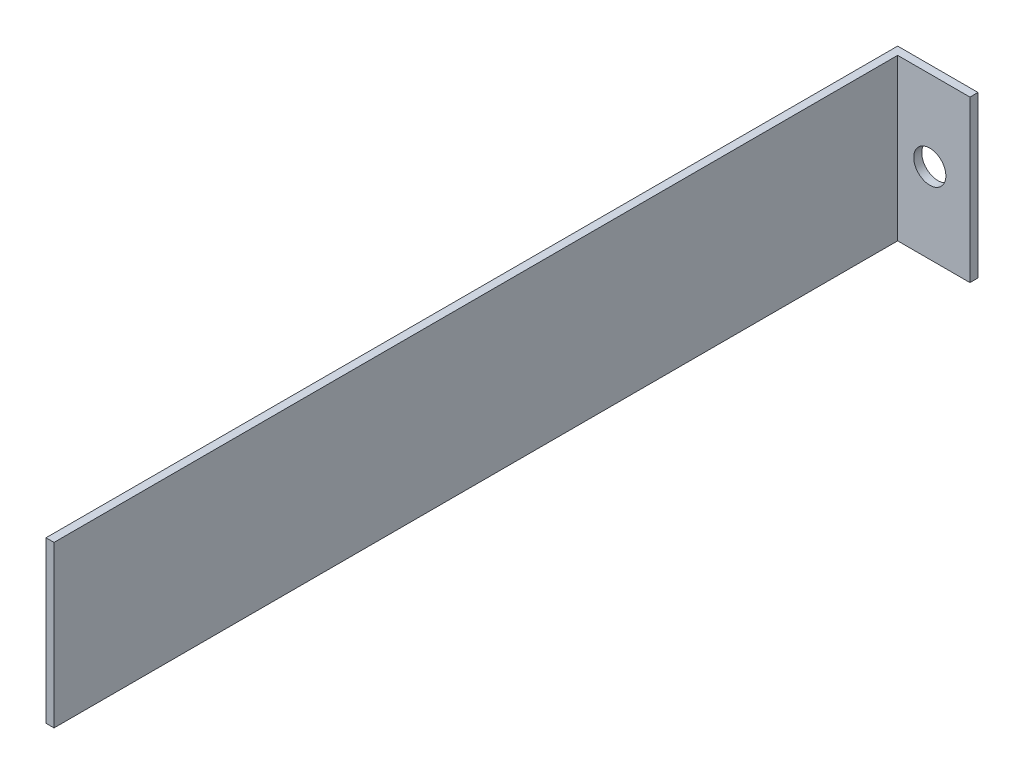
SolidWorks part; units mm, degrees
ref_plane "前视基准面" through (0, 0, 0) normal (0, 0, 1) x (1, 0, 0)
ref_plane "上视基准面" through (0, 0, 0) normal (0, 1, 0) x (1, 0, 0)
ref_plane "右视基准面" through (0, 0, 0) normal (1, 0, 0) x (0, 0, -1)
sketch "草图1" plane through (0, 0, 0) normal (0, 0, 1) x (1, 0, 0)
  line L0 (-37.1175, 25.838) -> (-17.1175, 25.838)
  line L1 (-17.1175, 25.838) -> (-17.1175, -14.162)
  line L2 (-17.1175, -14.162) -> (-37.1175, -14.162)
  line L3 (-37.1175, -14.162) -> (-37.1175, 25.838)
  line L4 (-27.1175, 25.838) -> (-27.1175, -14.162) construction
  circle A0 centre (-27.1175, 5.838) radius 4
  dimension "D3" = 8
  dimension "D1" = 20
  dimension "D2" = 40
extrude "凸台-拉伸1" add sketch "草图1" along normal blind 2
sketch "草图2" plane through (0, 0, 2) normal (0, 0, 1) x (1, 0, 0)
  line L0 (-37.1175, 25.838) -> (-35.1175, 25.838)
  line L1 (-17.1175, 25.838) -> (-37.1175, 25.838) construction
  line L2 (-35.1175, 25.838) -> (-35.1175, -14.162)
  line L3 (-37.1175, -14.162) -> (-17.1175, -14.162) construction
  line L4 (-35.1175, -14.162) -> (-37.1175, -14.162)
  line L5 (-37.1175, -14.162) -> (-37.1175, 25.838)
  dimension "D1" = 2
extrude "凸台-拉伸2" add sketch "草图2" along normal blind 210
